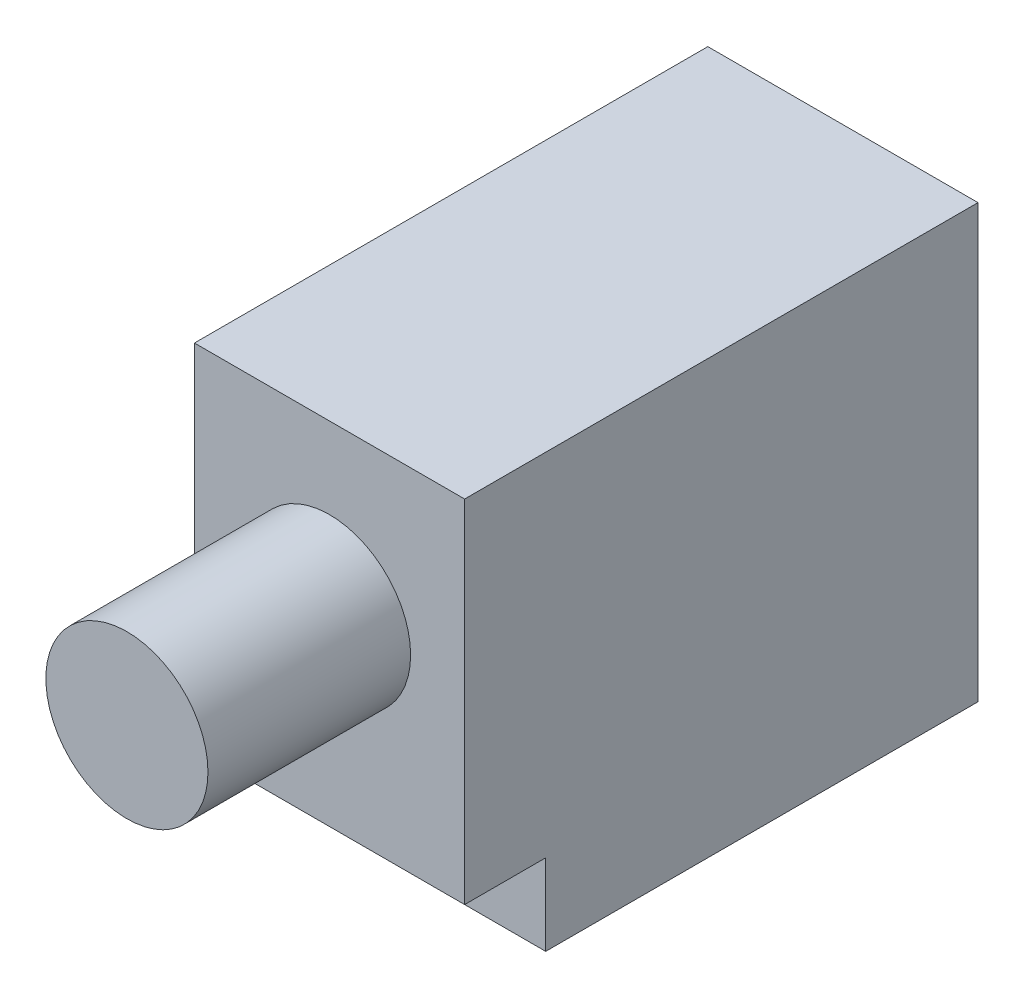
SolidWorks part; units mm, degrees
material "Plain Carbon Steel"
ref_plane "Front" through (0, 0, 0) normal (0, 0, 1) x (1, 0, 0)
ref_plane "Top" through (0, 0, 0) normal (0, 1, 0) x (1, 0, 0)
ref_plane "Right" through (0, 0, 0) normal (1, 0, 0) x (0, 0, -1)
sketch "Sketch1" plane through (0, 0, 0) normal (1, 0, 0) x (0, 0, -1)
  line L1 (-15.0813, 12.7) -> (15.0812, 12.7)
  line L2 (-15.0813, 12.7) -> (-15.0812, -12.7)
  line L3 (-15.0812, -12.7) -> (15.0812, -12.7)
  line L4 (15.0812, 12.7) -> (15.0812, -12.7)
  line L5 (-15.0813, 12.7) -> (15.0812, -12.7) construction
  line L6 (-15.0812, -12.7) -> (15.0812, 12.7) construction
  point P0 (0, 0)
  dimension "D1" = 30.1625
  dimension "D2" = 25.4
extrude "Boss-Extrude1" add sketch "Sketch1" along normal blind 15.875
sketch "Sketch2" plane through (0, 0, 15.0813) normal (0, 0, 1) x (1, 0, 0)
  line L0 (15.875, 12.7) -> (0, 12.7) construction
  circle A0 centre (7.9375, 3.175) radius 4.7625
  point P4 (7.9375, 12.7)
  dimension "D1" = 9.525
  dimension "D2" = 9.525
extrude "Boss-Extrude2" add sketch "Sketch2" along normal blind 11.9062
sketch "Sketch3" plane through (15.875, 0, 0) normal (1, 0, 0) x (0, 0, -1)
  line L1 (-15.0812, -12.7) -> (-10.3187, -12.7)
  line L2 (-15.0812, -12.7) -> (-15.0812, -7.9375)
  line L3 (-15.0812, -7.9375) -> (-10.3187, -7.9375)
  line L4 (-10.3187, -12.7) -> (-10.3187, -7.9375)
  dimension "D1" = 4.7625
extrude "Cut-Extrude1" cut sketch "Sketch3" against normal through all
equation "\"Total Cutting Length\"= \"Cutting Length-Outer\" + \"Cutting Length-Inner\""
equation "\"Amount in ft^2\"= \"Bounding Box Area-Blank\" / 144"
